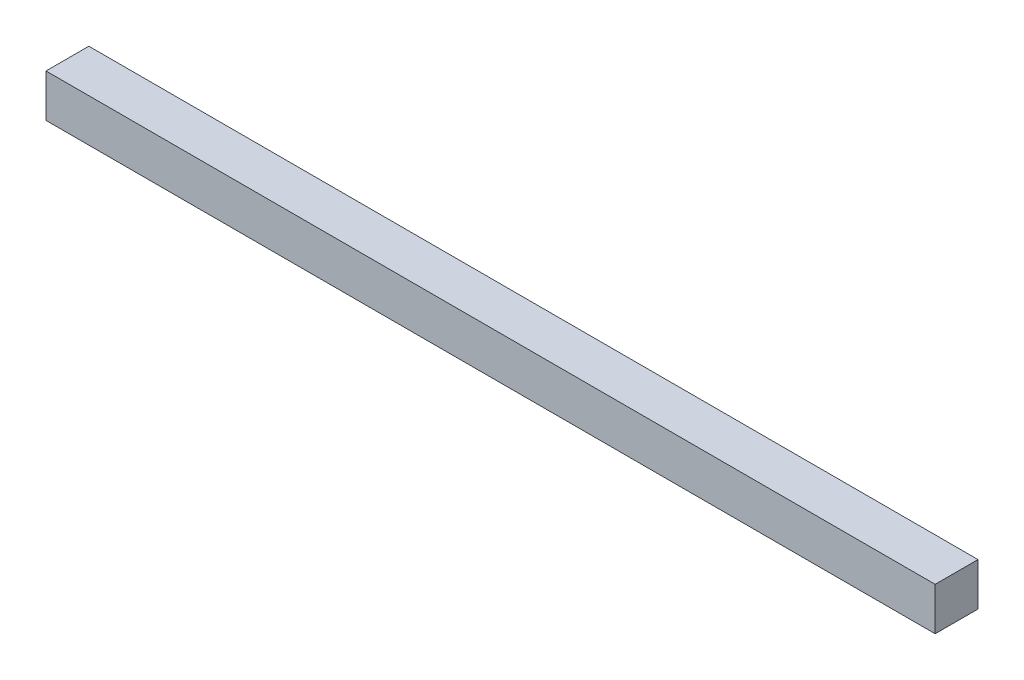
SolidWorks part; units mm, degrees
ref_plane "Front Plane" through (0, 0, 0) normal (0, 0, 1) x (1, 0, 0)
ref_plane "Top Plane" through (0, 0, 0) normal (0, 1, 0) x (1, 0, 0)
ref_plane "Right Plane" through (0, 0, 0) normal (1, 0, 0) x (0, 0, -1)
sketch "Sketch1" plane through (0, 0, 0) normal (0, 1, 0) x (1, 0, 0)
  line L1 (0, 0) -> (103.75, 0)
  line L2 (0, 0) -> (0, 5)
  line L3 (0, 5) -> (103.75, 5)
  line L4 (103.75, 0) -> (103.75, 5)
  dimension "D1" = 5
  dimension "D2" = 103.75
extrude "Boss-Extrude1" add sketch "Sketch1" along normal blind 5
